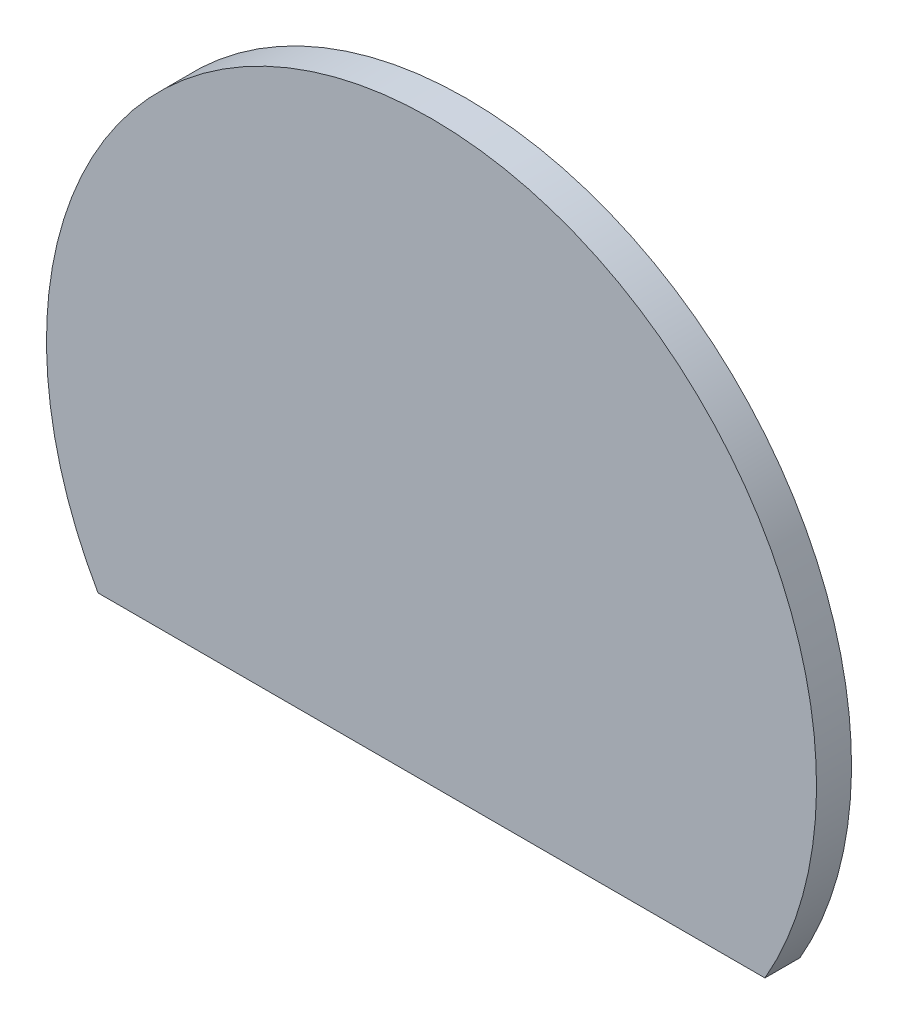
SolidWorks part; units mm, degrees
ref_plane "Front Plane" through (0, 0, 0) normal (0, 0, 1) x (1, 0, 0)
ref_plane "Top Plane" through (0, 0, 0) normal (0, 1, 0) x (1, 0, 0)
ref_plane "Right Plane" through (0, 0, 0) normal (1, 0, 0) x (0, 0, -1)
sketch "Sketch1" plane through (0, 0, 0) normal (0, 0, 1) x (1, 0, 0)
  line L0 (-9.5263, -5.5) -> (9.5263, -5.5)
  arc A0 (9.5263, -5.5) -> (-9.5263, -5.5) centre (0, 0) ccw
  circle A1 centre (0, 0) radius 4.5
  circle A2 centre (0, 0) radius 5.5
  dimension "D1" = 22
  dimension "D2" = 9
  dimension "D3" = 1
extrude "Boss-Extrude1" add sketch "Sketch1" along normal blind 1 contours L0 A2 A0 | A1 | A2 A1
sketch "Sketch3" plane through (0, 0, 0) normal (0, 0, -1) x (-1, 0, 0)
  circle A0 centre (0, 0) radius 3.5
  circle A1 centre (0, 0) radius 4.5
extrude "Boss-Extrude2" add sketch "Sketch3" along normal blind 2.2
sketch "Sketch4" plane through (0, 0, 0) normal (0, 0, -1) x (-1, 0, 0)
  circle A0 centre (0, 0) radius 1.4
extrude "Boss-Extrude3" add sketch "Sketch4" along normal blind 3 contours A0
